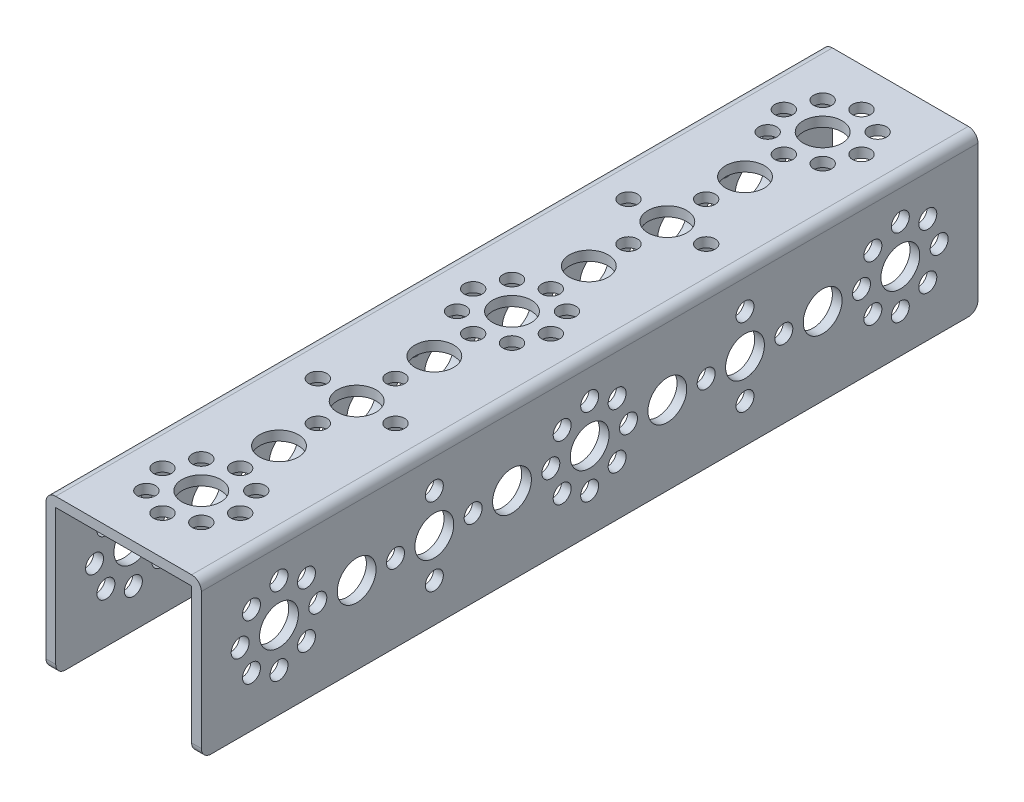
SolidWorks part; units mm, degrees
ref_plane "Front Plane" through (0, 0, 0) normal (0, 0, 1) x (1, 0, 0)
ref_plane "Top Plane" through (0, 0, 0) normal (0, 1, 0) x (1, 0, 0)
ref_plane "Right Plane" through (0, 0, 0) normal (1, 0, 0) x (0, 0, -1)
sketch "Sketch1" plane through (0, 0, 0) normal (0, 0, 1) x (1, 0, 0)
  line L0 (14, -16) -> (16, -16)
  line L1 (-16, 16) -> (16, 16)
  line L2 (-16, 16) -> (-16, -16)
  line L3 (-16, -16) -> (-14, -16)
  line L4 (16, 16) -> (16, -16)
  line L5 (-16, 16) -> (16, -16) construction
  line L6 (-16, -16) -> (16, 16) construction
  line L7 (-14, 14) -> (14, 14)
  line L8 (-14, 14) -> (-14, -16)
  line L10 (14, 14) -> (14, -16)
  point P0 (0, 0)
  dimension "D1" = 32
  dimension "D2" = 32
  dimension "D3" = 2
  dimension "D4" = 2
extrude "Boss-Extrude1" add sketch "Sketch1" against normal blind 160
sketch "Sketch2" plane through (0, 16, 0) normal (0, 1, 0) x (1, 0, 0)
  line L0 (0, 0) -> (0, 165.6972) construction
  line L1 (16, 0) -> (-16, 0) construction
  line L2 (-22.0589, 80) -> (32.6471, 80) construction
  circle B0 centre (0, 32) radius 4
  circle B1 centre (0, 64) radius 4
  circle B2 centre (-0.1754, 96) radius 4
  circle B3 centre (0, 128) radius 4
  circle B4 centre (0, 48) radius 4
  circle B5 centre (0, 56) radius 1.85
  circle B6 centre (0, 40) radius 1.85
  circle B7 centre (8, 48) radius 1.85
  circle B8 centre (-8, 48) radius 1.85
  circle B9 centre (0, 24) radius 1.85
  circle B10 centre (8, 16) radius 1.85
  circle B11 centre (0, 16) radius 4
  circle B12 centre (-8, 16) radius 1.85
  circle B13 centre (-5.66, 10.34) radius 1.85
  circle B14 centre (5.66, 10.34) radius 1.85
  circle B15 centre (0, 8) radius 1.85
  circle B16 centre (-5.66, 21.66) radius 1.85
  circle B17 centre (5.66, 21.66) radius 1.85
  circle B18 centre (0, 112) radius 4
  circle B19 centre (0, 120) radius 1.85
  circle B20 centre (0, 104) radius 1.85
  circle B21 centre (8, 112) radius 1.85
  circle B22 centre (-8, 112) radius 1.85
  circle B23 centre (0, 88) radius 1.85
  circle B24 centre (8, 80) radius 1.85
  circle B25 centre (0, 80) radius 4
  circle B26 centre (-8, 80) radius 1.85
  circle B27 centre (-5.66, 74.34) radius 1.85
  circle B28 centre (5.66, 74.34) radius 1.85
  circle B29 centre (0, 72) radius 1.85
  circle B30 centre (-5.66, 85.66) radius 1.85
  circle B31 centre (5.66, 85.66) radius 1.85
  circle B32 centre (0, 136) radius 1.85
  circle B33 centre (-8, 144) radius 1.85
  circle B34 centre (0, 144) radius 4
  circle B35 centre (8, 144) radius 1.85
  circle B36 centre (5.66, 149.66) radius 1.85
  circle B37 centre (-5.66, 149.66) radius 1.85
  circle B38 centre (0, 152) radius 1.85
  circle B39 centre (5.66, 138.34) radius 1.85
  circle B40 centre (-5.66, 138.34) radius 1.85
sketch_block_instance "TETRIX 160 Pattern-1"
sketch_block "TETRIX 160 Pattern" parameters "D1"=16, "D2"=16, "D3"=16, "D4"=16, "D5"=16, "D6"=16, "D7"=16, "D8"=16
extrude "Cut-Extrude1" cut sketch "Sketch2" against normal through all
sketch "Sketch3" plane through (16, 0, 0) normal (1, 0, 0) x (0, 0, -1)
  line L0 (-3.4954, 0) -> (176.3323, 0) construction
  line L1 (80, 24.2278) -> (80, -20.5542) construction
  circle B0 centre (32, 0) radius 4
  circle B1 centre (64, 0) radius 4
  circle B2 centre (96, 0.1754) radius 4
  circle B3 centre (128, 0) radius 4
  circle B4 centre (48, 0) radius 4
  circle B5 centre (56, 0) radius 1.85
  circle B6 centre (40, 0) radius 1.85
  circle B7 centre (48, -8) radius 1.85
  circle B8 centre (48, 8) radius 1.85
  circle B9 centre (24, 0) radius 1.85
  circle B10 centre (16, -8) radius 1.85
  circle B11 centre (16, 0) radius 4
  circle B12 centre (16, 8) radius 1.85
  circle B13 centre (10.34, 5.66) radius 1.85
  circle B14 centre (10.34, -5.66) radius 1.85
  circle B15 centre (8, 0) radius 1.85
  circle B16 centre (21.66, 5.66) radius 1.85
  circle B17 centre (21.66, -5.66) radius 1.85
  circle B18 centre (112, 0) radius 4
  circle B19 centre (120, 0) radius 1.85
  circle B20 centre (104, 0) radius 1.85
  circle B21 centre (112, -8) radius 1.85
  circle B22 centre (112, 8) radius 1.85
  circle B23 centre (88, 0) radius 1.85
  circle B24 centre (80, -8) radius 1.85
  circle B25 centre (80, 0) radius 4
  circle B26 centre (80, 8) radius 1.85
  circle B27 centre (74.34, 5.66) radius 1.85
  circle B28 centre (74.34, -5.66) radius 1.85
  circle B29 centre (72, 0) radius 1.85
  circle B30 centre (85.66, 5.66) radius 1.85
  circle B31 centre (85.66, -5.66) radius 1.85
  circle B32 centre (136, 0) radius 1.85
  circle B33 centre (144, 8) radius 1.85
  circle B34 centre (144, 0) radius 4
  circle B35 centre (144, -8) radius 1.85
  circle B36 centre (149.66, -5.66) radius 1.85
  circle B37 centre (149.66, 5.66) radius 1.85
  circle B38 centre (152, 0) radius 1.85
  circle B39 centre (138.34, -5.66) radius 1.85
  circle B40 centre (138.34, 5.66) radius 1.85
sketch_block_instance "TETRIX 160 Pattern-1"
extrude "Cut-Extrude2" cut sketch "Sketch3" against normal through all
fillet "Fillet1" radius 2 6 edges at (-15, -16, -160) (15, -16, -160) (-15, -16, 0) (15, -16, 0) (-16, 16, -80) (16, 16, -80)
